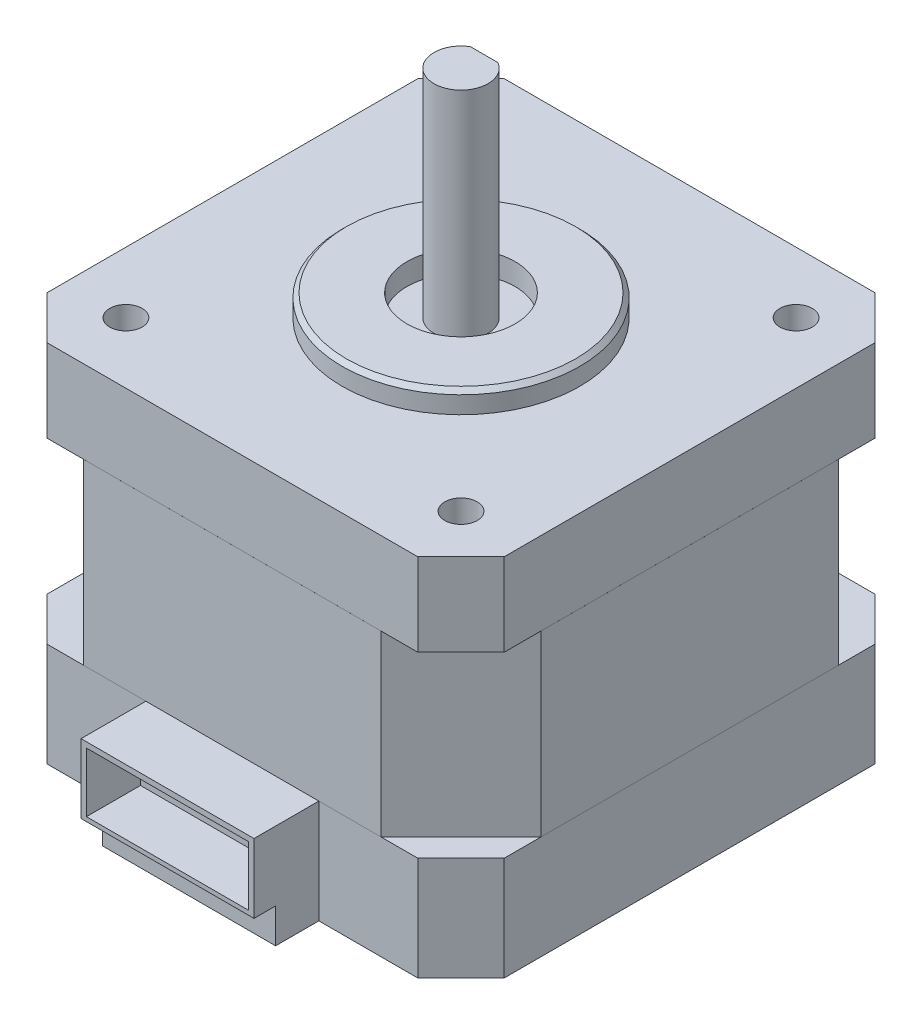
SolidWorks part; units mm, degrees
ref_plane "Front" through (0, 0, 0) normal (0, 0, 1) x (1, 0, 0)
ref_plane "Top" through (0, 0, 0) normal (0, 1, 0) x (1, 0, 0)
ref_plane "Right" through (0, 0, 0) normal (1, 0, 0) x (0, 0, -1)
sketch "Sketch1" plane through (0, 0, 0) normal (0, 1, 0) x (1, 0, 0)
  line L1 (-21.15, 21.15) -> (21.15, 21.15)
  line L2 (-21.15, 21.15) -> (-21.15, -21.15)
  line L3 (-21.15, -21.15) -> (21.15, -21.15)
  line L4 (21.15, 21.15) -> (21.15, -21.15)
  line L7 (0, 20) -> (0, -20) construction
  line L8 (20, 0) -> (-20, 0) construction
  line L10 (-55, 0) -> (55, 0) construction
  line L11 (0, -55) -> (0, 55) construction
  dimension "D1" = 42.3
extrude "Extrude1" add sketch "Sketch1" along normal blind 9.6 from offset 17 offset against normal yes
chamfer "Chamfer3" distance 4 angle 45 4 edges at (21.15, -12.2, 21.15) (-21.15, -12.2, 21.15) (21.15, -12.2, -21.15) (-21.15, -12.2, -21.15)
sketch "Sketch31" plane through (0, -7.4, 0) normal (0, 1, 0) x (1, 0, 0)
  line L0 (0, 21.15) -> (-13.75, 21.15) construction
  line L1 (17.15, 21.15) -> (-17.15, 21.15) construction
  line L2 (-13.75, 21.15) -> (13.75, 21.15)
  line L3 (-13.75, 21.15) -> (-21.15, 13.75)
  line L4 (-21.15, 17.15) -> (-21.15, -17.15) construction
  line L5 (13.75, 21.15) -> (21.15, 13.75)
  line L6 (21.15, -17.15) -> (21.15, 17.15) construction
  line L7 (-21.15, 0) -> (21.15, 0) construction
  line L8 (0, -21.15) -> (-13.75, -21.15) construction
  line L9 (13.75, -21.15) -> (21.15, -13.75)
  line L10 (-13.75, -21.15) -> (-21.15, -13.75)
  line L11 (-13.75, -21.15) -> (13.75, -21.15)
  line L12 (-21.15, 13.75) -> (-21.15, -13.75)
  line L13 (21.15, 13.75) -> (21.15, -13.75)
  dimension "D1" = 13.75
  dimension "D2" = 27.5
  dimension "D3" = 10.4652
extrude "Boss-Extrude8" add sketch "Sketch31" along normal blind 16.5
sketch "Sketch32" plane through (0, 9.1, 0) normal (0, 1, 0) x (1, 0, 0)
  line L0 (-17.15, 21.15) -> (-21.15, 17.15) construction
  line L1 (-13.75, 21.15) -> (-17.15, 21.15) construction
  line L2 (13.75, 21.15) -> (-13.75, 21.15) construction
  line L3 (17.15, 21.15) -> (13.75, 21.15) construction
  line L4 (21.15, 17.15) -> (17.15, 21.15) construction
  line L5 (21.15, 13.75) -> (21.15, 17.15) construction
  line L6 (21.15, -13.75) -> (21.15, 13.75) construction
  line L7 (-21.15, 17.15) -> (-21.15, 13.75) construction
  line L8 (-21.15, 13.75) -> (-21.15, -13.75) construction
  line L9 (21.15, -17.15) -> (21.15, -13.75) construction
  line L10 (17.15, -21.15) -> (21.15, -17.15) construction
  line L11 (13.75, -21.15) -> (17.15, -21.15) construction
  line L12 (-13.75, -21.15) -> (13.75, -21.15) construction
  line L13 (-17.15, -21.15) -> (-13.75, -21.15) construction
  line L14 (-21.15, -17.15) -> (-17.15, -21.15) construction
  line L15 (-21.15, -13.75) -> (-21.15, -17.15) construction
  line L16 (-17.15, 21.15) -> (-21.15, 17.15)
  line L17 (-13.75, 21.15) -> (-17.15, 21.15)
  line L18 (13.75, 21.15) -> (-13.75, 21.15)
  line L19 (17.15, 21.15) -> (13.75, 21.15)
  line L20 (21.15, 17.15) -> (17.15, 21.15)
  line L21 (21.15, 13.75) -> (21.15, 17.15)
  line L22 (21.15, -13.75) -> (21.15, 13.75)
  line L23 (-21.15, 17.15) -> (-21.15, 13.75)
  line L24 (-21.15, 13.75) -> (-21.15, -13.75)
  line L25 (21.15, -17.15) -> (21.15, -13.75)
  line L26 (17.15, -21.15) -> (21.15, -17.15)
  line L27 (13.75, -21.15) -> (17.15, -21.15)
  line L28 (-13.75, -21.15) -> (13.75, -21.15)
  line L29 (-17.15, -21.15) -> (-13.75, -21.15)
  line L30 (-21.15, -17.15) -> (-17.15, -21.15)
  line L31 (-21.15, -13.75) -> (-21.15, -17.15)
extrude "Boss-Extrude9" add sketch "Sketch32" along normal blind 7.65
sketch "Sketch33" plane through (0, 16.75, 0) normal (0, 1, 0) x (1, 0, 0)
  line L0 (-19.15, 19.15) -> (19.15, -19.15) construction
  line L1 (-17.15, 21.15) -> (-21.15, 17.15) construction
  line L2 (17.15, -21.15) -> (21.15, -17.15) construction
  circle A0 centre (0, 0) radius 11
  dimension "D1" = 22
extrude "Boss-Extrude10" add sketch "Sketch33" along normal blind 2
sketch "Sketch34" plane through (0, 18.75, 0) normal (0, 1, 0) x (1, 0, 0)
  circle A0 centre (0, 0) radius 5
  dimension "D1" = 10
extrude "Cut-Extrude1" cut sketch "Sketch34" against normal blind 2
sketch "Sketch35" plane through (0, 16.75, 0) normal (0, 1, 0) x (1, 0, 0)
  circle A0 centre (0, 0) radius 2.5
  dimension "D1" = 5
extrude "Boss-Extrude11" add sketch "Sketch35" along normal blind 20
sketch "Sketch36" plane through (0, 36.75, 0) normal (0, 1, 0) x (1, 0, 0)
  line L0 (0, -2.5) -> (0, 2.15)
  line L1 (-1.2757, 2.15) -> (1.2757, 2.15)
  circle A0 centre (0, 0) radius 2.5 construction
  circle A1 centre (0, 0) radius 2.5 construction
  circle A2 centre (0, 0) radius 2.5
  circle M1 centre (0, 0) radius 2.5
  dimension "D1" = 4.65
extrude "Cut-Extrude3" cut sketch "Sketch36" against normal blind 15 contours L1 M1
sketch "Sketch37" plane through (21.15, 0, 0) normal (1, 0, 0) x (0, 0, -1)
  line L0 (-13.75, 9.1) -> (13.75, 9.1)
  line L1 (13.75, 9.1) -> (13.75, -7.4)
  line L2 (13.75, -7.4) -> (-13.75, -7.4)
  line L3 (-13.75, -7.4) -> (-13.75, 9.1)
extrude "Boss-Extrude12" add sketch "Sketch37" along normal blind 0.001
sketch "Sketch38" plane through (0, 0, 21.15) normal (0, 0, 1) x (1, 0, 0)
  line L1 (-13.75, 9.1) -> (13.75, 9.1)
  line L2 (-13.75, 9.1) -> (-13.75, -7.4)
  line L3 (-13.75, -7.4) -> (13.75, -7.4)
  line L4 (13.75, 9.1) -> (13.75, -7.4)
extrude "Boss-Extrude13" add sketch "Sketch38" along normal blind 0.001
sketch "Sketch39" plane through (-21.15, 0, 0) normal (-1, 0, 0) x (0, 0, 1)
  line L1 (-13.75, 9.1) -> (13.75, 9.1)
  line L2 (-13.75, 9.1) -> (-13.75, -7.4)
  line L3 (-13.75, -7.4) -> (13.75, -7.4)
  line L4 (13.75, 9.1) -> (13.75, -7.4)
extrude "Boss-Extrude14" add sketch "Sketch39" along normal blind 0.001
sketch "Sketch40" plane through (0, 0, -21.15) normal (0, 0, -1) x (-1, 0, 0)
  line L1 (-13.75, 9.1) -> (13.75, 9.1)
  line L2 (-13.75, 9.1) -> (-13.75, -7.4)
  line L3 (-13.75, -7.4) -> (13.75, -7.4)
  line L4 (13.75, 9.1) -> (13.75, -7.4)
extrude "Boss-Extrude15" add sketch "Sketch40" along normal blind 0.001
sketch "Sketch41" plane through (0, 16.75, 0) normal (0, 1, 0) x (1, 0, 0)
  line L0 (0, 21.15) -> (0, -21.15) construction
  line L1 (-21.15, 17.15) -> (-21.15, -17.15) construction
  line L2 (-21.15, 0) -> (-15.5, 0) construction
  line L3 (-15.5, 0) -> (-15.5, 15.5) construction
  line L4 (17.15, 21.15) -> (-17.15, 21.15) construction
  line L5 (-17.15, -21.15) -> (17.15, -21.15) construction
  circle A0 centre (-15.5, 15.5) radius 1.5
  circle A1 centre (-15.5, -15.5) radius 1.5
  circle A2 centre (15.5, -15.5) radius 1.5
  circle A3 centre (15.5, 15.5) radius 1.5
  dimension "D1" = 3
  dimension "D2" = 15.5
  dimension "D3" = 5.65
extrude "Cut-Extrude4" cut sketch "Sketch41" against normal blind 6
sketch "Sketch42" plane through (0, -17, 0) normal (0, -1, 0) x (1, 0, 0)
  circle A0 centre (0, 0) radius 4.5
  circle A1 centre (-15.5, 15.5) radius 1.5 construction
  circle A2 centre (15.5, 15.5) radius 1.5 construction
  circle A3 centre (15.5, -15.5) radius 1.5 construction
  circle A4 centre (-15.5, -15.5) radius 1.5 construction
  circle A5 centre (-15.5, 15.5) radius 1.5
  circle A6 centre (15.5, 15.5) radius 1.5
  circle A7 centre (15.5, -15.5) radius 1.5
  circle A8 centre (-15.5, -15.5) radius 1.5
  dimension "D1" = 9
extrude "Cut-Extrude5" cut sketch "Sketch42" against normal blind 3
sketch "Sketch43" plane through (0, -17, 0) normal (0, -1, 0) x (1, 0, 0)
  line L0 (0, 21.15) -> (8, 21.15) construction
  line L1 (-17.15, 21.15) -> (17.15, 21.15) construction
  line L3 (8, 21.15) -> (-8, 21.15)
  line L4 (8, 21.15) -> (8, 25.15)
  line L5 (8, 25.15) -> (-8, 25.15)
  line L6 (-8, 21.15) -> (-8, 25.15)
  dimension "D1" = 8
  dimension "D2" = 16
  dimension "D3" = 4
extrude "Boss-Extrude16" add sketch "Sketch43" against normal blind 3.2
sketch "Sketch44" plane through (0, 0, 21.15) normal (0, 0, 1) x (1, 0, 0)
  line L1 (8, -13.8) -> (-8, -13.8)
  line L2 (8, -13.8) -> (8, -7.4)
  line L3 (8, -7.4) -> (-8, -7.4)
  line L4 (-8, -13.8) -> (-8, -7.4)
  dimension "D1" = 16
  dimension "D2" = 6.4
extrude "Boss-Extrude17" add sketch "Sketch44" along normal blind 6
sketch "Sketch45" plane through (0, 0, 27.15) normal (0, 0, 1) x (1, 0, 0)
  line L0 (-8, -7.4) -> (-7.5, -7.4) construction
  line L1 (8, -7.4) -> (-8, -7.4) construction
  line L2 (-7.5, -7.4) -> (-7.5, -7.9) construction
  line L4 (-7.5, -7.9) -> (7.5, -7.9)
  line L5 (-7.5, -7.9) -> (-7.5, -13.4)
  line L6 (-7.5, -13.4) -> (7.5, -13.4)
  line L7 (7.5, -7.9) -> (7.5, -13.4)
  dimension "D1" = 0.5
  dimension "D2" = 0.5
  dimension "D3" = 5.5
  dimension "D4" = 15
extrude "Cut-Extrude6" cut sketch "Sketch45" against normal blind 5
sketch "Sketch46" plane through (0, 10.75, 0) normal (0, 1, 0) x (1, 0, 0)
  circle A0 centre (-15.5, -15.5) radius 1.5
  circle A1 centre (-15.5, 15.5) radius 1.5 construction
  circle A2 centre (15.5, 15.5) radius 1.5 construction
  circle A3 centre (15.5, -15.5) radius 1.5 construction
  circle A4 centre (-15.5, 15.5) radius 1.5
  circle A5 centre (15.5, 15.5) radius 1.5
  circle A6 centre (15.5, -15.5) radius 1.5
extrude "Boss-Extrude18" add sketch "Sketch46" along normal blind 1.5
chamfer "Chamfer4" distance 0.4 angle 45 1 edges at (0, 18.75, 11)
